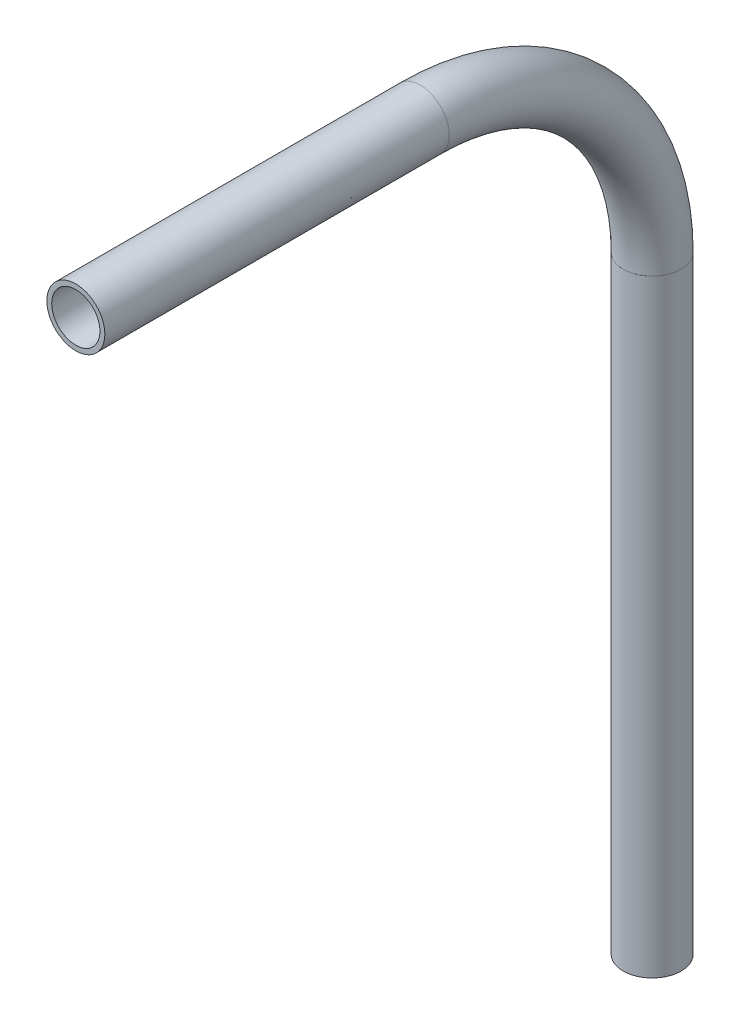
SolidWorks part; units mm, degrees
ref_plane "Front Plane" through (0, 0, 0) normal (0, 0, 1) x (1, 0, 0)
ref_plane "Top Plane" through (0, 0, 0) normal (0, 1, 0) x (1, 0, 0)
ref_plane "Right Plane" through (0, 0, 0) normal (1, 0, 0) x (0, 0, -1)
sketch "Sketch1" plane through (0, 0, 0) normal (1, 0, 0) x (0, 0, -1)
  line L0 (-310.1301, 1009.7478) -> (-310.1301, 1142.8807)
  line L1 (-436.365, 1193.6807) -> (-360.9301, 1193.6807)
  arc A0 (-310.1301, 1142.8807) -> (-360.9301, 1193.6807) centre (-360.9301, 1142.8807) ccw
  point P5 (-360.9301, 1193.6807)
  dimension "D1" = 50.8
other "Pipe 0.5 SCH 40(1)"
ref_plane "Plane1" through (0, 1009.7478, 310.1301) normal (0, 1, 0) x (0, 0, 1)
sketch "Sketch11" plane through (0, 1009.7478, 310.1301) normal (0, 1, 0) x (0, 0, 1)
  circle A0 centre (0, 0) radius 5.2832
  circle A1 centre (0, 0) radius 6.35
  point P5 (0, 0)
  dimension "In_dia" = 10.5664
  dimension "Out_dia" = 12.7
